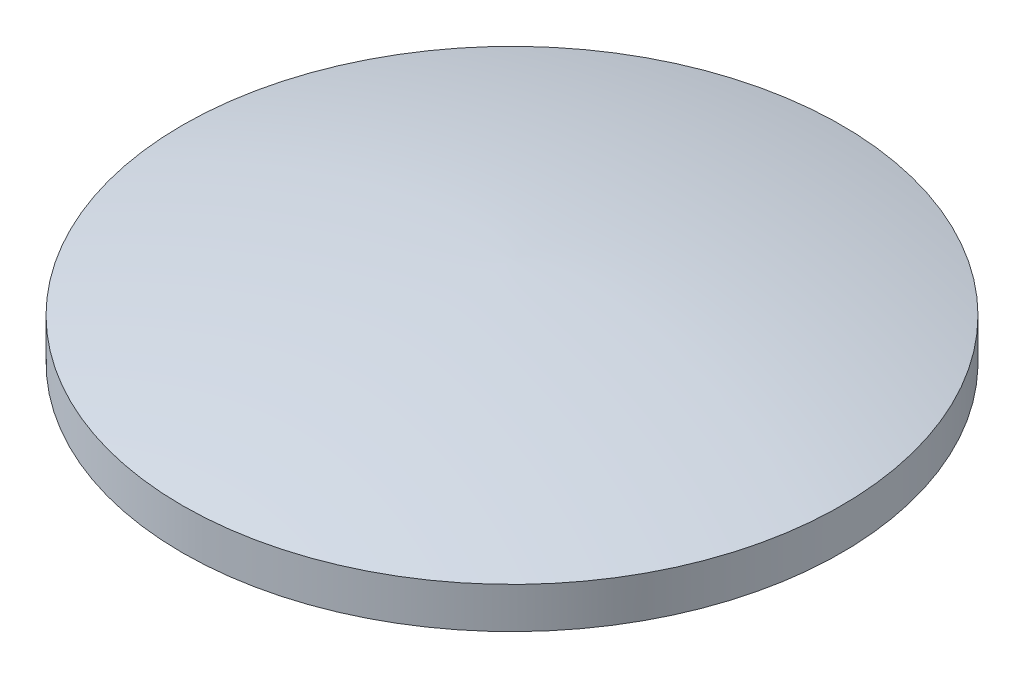
SolidWorks part; units mm, degrees
ref_plane "Front Plane" through (0, 0, 0) normal (0, 0, 1) x (1, 0, 0)
ref_plane "Top Plane" through (0, 0, 0) normal (0, 1, 0) x (1, 0, 0)
ref_plane "Right Plane" through (0, 0, 0) normal (1, 0, 0) x (0, 0, -1)
sketch "Sketch1" plane through (0, 0, 0) normal (0, 0, 1) x (1, 0, 0)
  line L0 (0, 4.807) -> (0, 5.807)
  line L1 (8.055, 6.9887) -> (8.055, 4.807)
  line L2 (0, 4.807) -> (8.055, 4.807)
  spline S0 degree 2 poles (0, 5.807) (3.932, 6.8969) (8.055, 6.9887) knots 0 0 0 1 1 1
  dimension "D1" = 8.055
  dimension "D2" = 1
revolve "Revolve1" add sketch "Sketch1" angle 360 about L1
